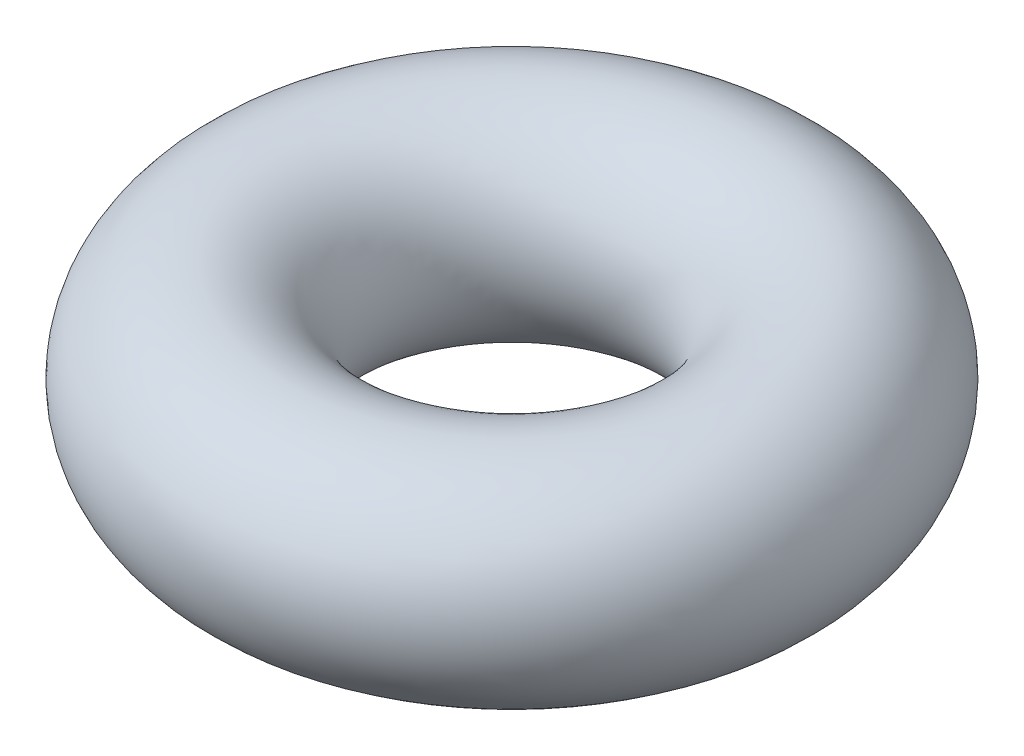
SolidWorks part; units mm, degrees
ref_plane "Plan de face" through (0, 0, 0) normal (0, 0, 1) x (1, 0, 0)
ref_plane "Plan de dessus" through (0, 0, 0) normal (0, 1, 0) x (1, 0, 0)
ref_plane "Plan de droite" through (0, 0, 0) normal (1, 0, 0) x (0, 0, -1)
sketch "Esquisse1" plane through (0, 0, 0) normal (0, 0, 1) x (1, 0, 0)
  line L0 (0, -2.3203) -> (0, 2.3203) construction
  circle A0 centre (2.0475, 0) radius 0.9525
  point P3 (3, 0)
  dimension "D2" = 1.905
  dimension "D1" = 6
revolve "Révolution1" add sketch "Esquisse1" angle 360 about L0
